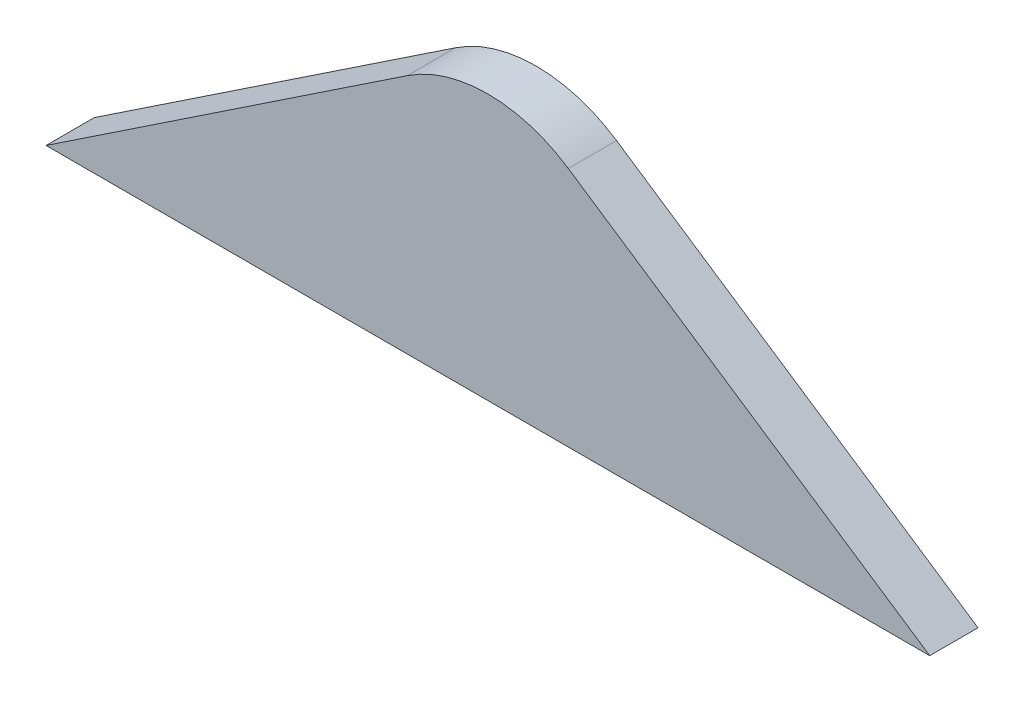
SolidWorks part; units mm, degrees
ref_plane "Płaszczyzna przednia" through (0, 0, 0) normal (0, 0, 1) x (1, 0, 0)
ref_plane "Płaszczyzna górna" through (0, 0, 0) normal (0, 1, 0) x (1, 0, 0)
ref_plane "Płaszczyzna prawa" through (0, 0, 0) normal (1, 0, 0) x (0, 0, -1)
sketch "Szkic1" plane through (0, 0, 0) normal (0, 0, 1) x (1, 0, 0)
  line L0 (0, 0) -> (183, 0)
  line L1 (91.5, 0) -> (91.5, 25) construction
  line L2 (0, 0) -> (74.8462, 49.953)
  line L3 (183, 0) -> (108.1538, 49.953)
  arc A1 (74.8462, 49.953) -> (108.1538, 49.953) centre (91.5, 25) cw
  dimension "D4" = 30
  dimension "D1" = 183
  dimension "D2" = 25
extrude "Dodanie-wyciągnięcie1" add sketch "Szkic1" along normal blind 10
